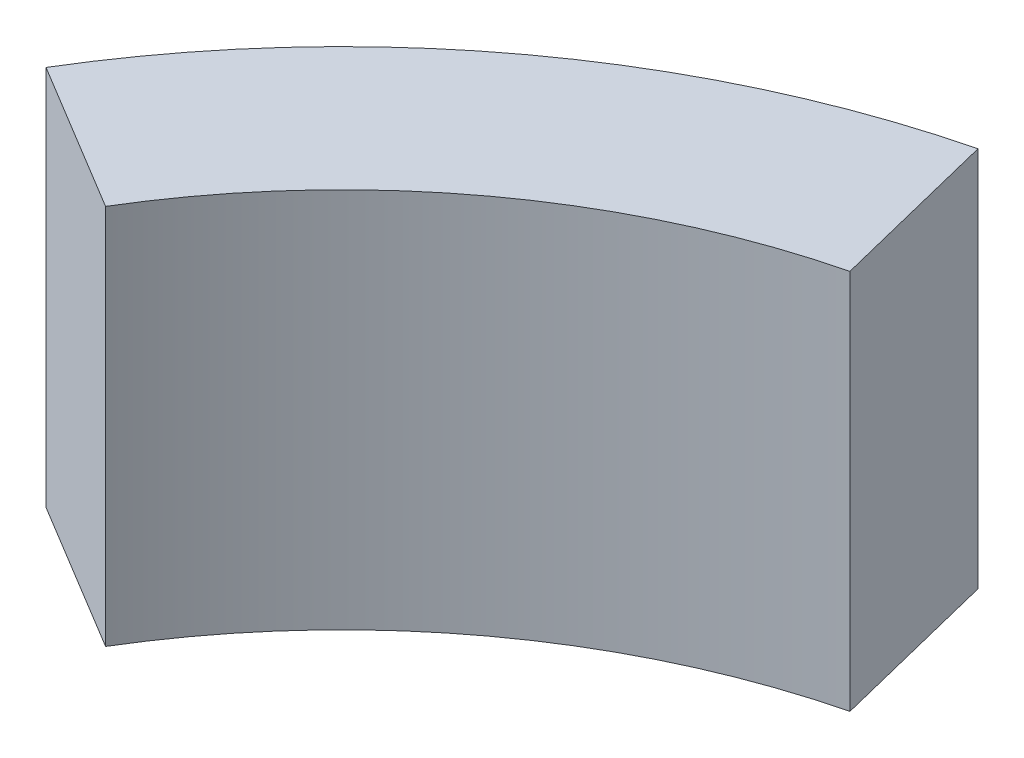
SolidWorks part; units mm, degrees
ref_plane "Front Plane" through (0, 0, 0) normal (0, 0, 1) x (1, 0, 0)
ref_plane "Top Plane" through (0, 0, 0) normal (0, 1, 0) x (1, 0, 0)
ref_plane "Right Plane" through (0, 0, 0) normal (1, 0, 0) x (0, 0, -1)
sketch "Sketch1" plane through (0, 0, 0) normal (0, 1, 0) x (1, 0, 0)
  line L0 (-23.4803, 14.161) -> (-18.7534, 11.3102)
  line L1 (-6.5897, 26.6164) -> (-5.2631, 21.2582)
  arc A0 (-23.4803, 14.161) -> (-6.5897, 26.6164) centre (0, 0) cw
  arc A1 (-18.7534, 11.3102) -> (-5.2631, 21.2582) centre (0, 0) cw
  dimension "D1" = 27.42
  dimension "D2" = 21.9
  dimension "D3" = 45
extrude "Boss-Extrude1" add sketch "Sketch1" along normal blind 12
